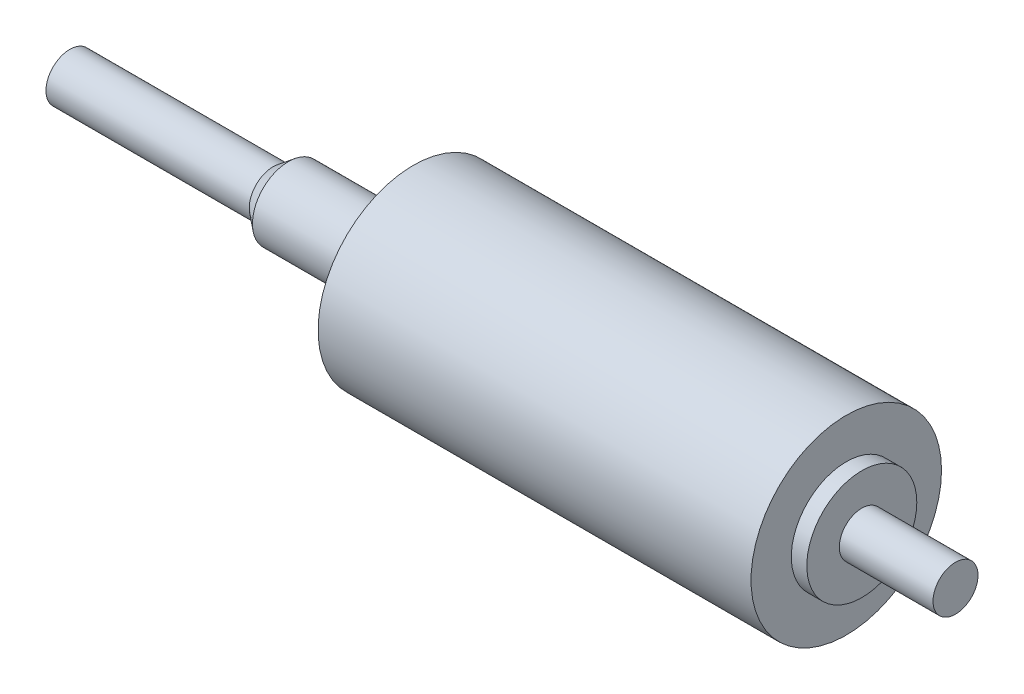
SolidWorks part; units mm, degrees
ref_plane "Front Plane" through (0, 0, 0) normal (0, 0, 1) x (1, 0, 0)
ref_plane "Top Plane" through (0, 0, 0) normal (0, 1, 0) x (1, 0, 0)
ref_plane "Right Plane" through (0, 0, 0) normal (1, 0, 0) x (0, 0, -1)
sketch "Sketch1" plane through (0, 0, 0) normal (0, 0, 1) x (1, 0, 0)
  line L1 (0, 6.2357) -> (28.3464, 6.2357)
  line L2 (28.3464, 6.2357) -> (28.3464, 3.6004)
  line L3 (28.3464, 3.6004) -> (29.3624, 3.6004)
  line L4 (29.3624, 3.6004) -> (29.3624, 1.4732)
  line L5 (29.3624, 1.4732) -> (35.4965, 1.4732)
  line L6 (35.4965, 1.4732) -> (35.4965, 0)
  line L7 (35.4965, 0) -> (0, 0)
  line L8 (0, 6.2357) -> (0, 2.3559)
  line L9 (0, 2.3559) -> (-8.1788, 2.3558)
  line L10 (-8.1788, 2.3558) -> (-9.1821, 1.5621)
  line L11 (-9.1821, 1.5621) -> (-22.4917, 1.5621)
  line L12 (-22.4917, 1.5621) -> (-22.4917, 0)
  line L13 (-22.4917, 0) -> (0, 0)
  dimension "D1" = 6.2357
  dimension "D2" = 1.4732
  dimension "D3" = 3.6004
  dimension "D4" = 28.3464
  dimension "D5" = 7.1501
  dimension "D6" = 1.016
  dimension "D7" = 22.4917
  dimension "D8" = 8.1788
  dimension "D9" = 13.3096
  dimension "D10" = 1.5621
  dimension "D11" = 2.3559
revolve "Revolve1" add sketch "Sketch1" angle 360 about L7
